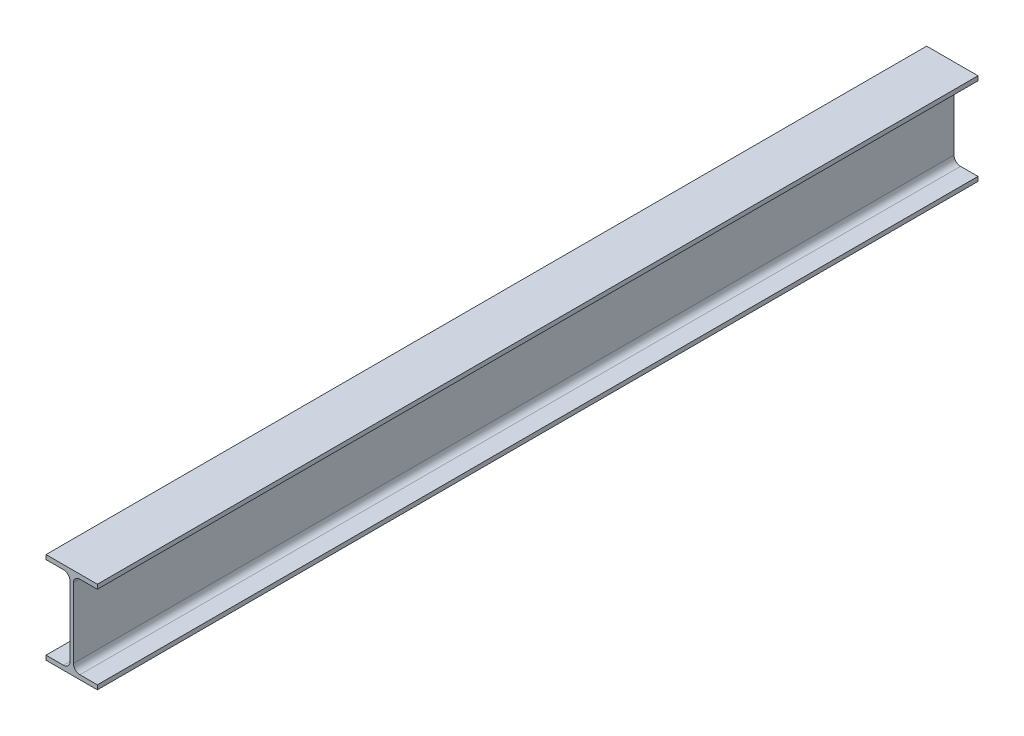
SolidWorks part; units mm, degrees
material "1.0035 (S185)"
ref_plane "Front Plane" through (0, 0, 0) normal (0, 0, 1) x (1, 0, 0)
ref_plane "Top Plane" through (0, 0, 0) normal (0, 1, 0) x (1, 0, 0)
ref_plane "Right Plane" through (0, 0, 0) normal (1, 0, 0) x (0, 0, -1)
sketch "Sketch1" plane through (0, 0, 0) normal (0, 0, 1) x (1, 0, 0)
  line L0 (-27.5, 49) -> (27.5, 49)
  line L1 (27.5, 49) -> (27.5, 44.3)
  line L2 (27.5, 44.3) -> (8.8, 44.3)
  line L3 (1.8, 37.3) -> (1.8, -37.3)
  line L4 (8.8, -44.3) -> (27.5, -44.3)
  line L5 (27.5, -44.3) -> (27.5, -49)
  line L6 (27.5, -49) -> (-27.5, -49)
  line L7 (-27.5, -49) -> (-27.5, -44.3)
  line L8 (-27.5, -44.3) -> (-8.8, -44.3)
  line L9 (-1.8, -37.3) -> (-1.8, 37.3)
  line L10 (-8.8, 44.3) -> (-27.5, 44.3)
  line L11 (-27.5, 44.3) -> (-27.5, 49)
  arc A0 (8.8, -44.3) -> (1.8, -37.3) centre (8.8, -37.3) cw
  arc A1 (-1.8, -37.3) -> (-8.8, -44.3) centre (-8.8, -37.3) cw
  arc A2 (-8.8, 44.3) -> (-1.8, 37.3) centre (-8.8, 37.3) cw
  arc A3 (1.8, 37.3) -> (8.8, 44.3) centre (8.8, 37.3) cw
  dimension "D8" = 7
  dimension "D2" = 3.6
  dimension "D3" = 4.7
  dimension "D4" = 4.7
  dimension "D5" = 1.8
  dimension "D6" = 55
  dimension "D7" = 25.7
  dimension "D1" = 98
  dimension "D9" = 49
extrude "Boss-Extrude1" add sketch "Sketch1" along normal blind 943
equation "\"D4@Sketch1\"=\"D3@Sketch1\""
equation "\"D5@Sketch1\"=\"D2@Sketch1\"/2"
equation "\"D7@Sketch1\"=(\"D6@Sketch1\"-\"D2@Sketch1\")/2"
equation "\"D9@Sketch1\"=\"D1@Sketch1\"/2"
